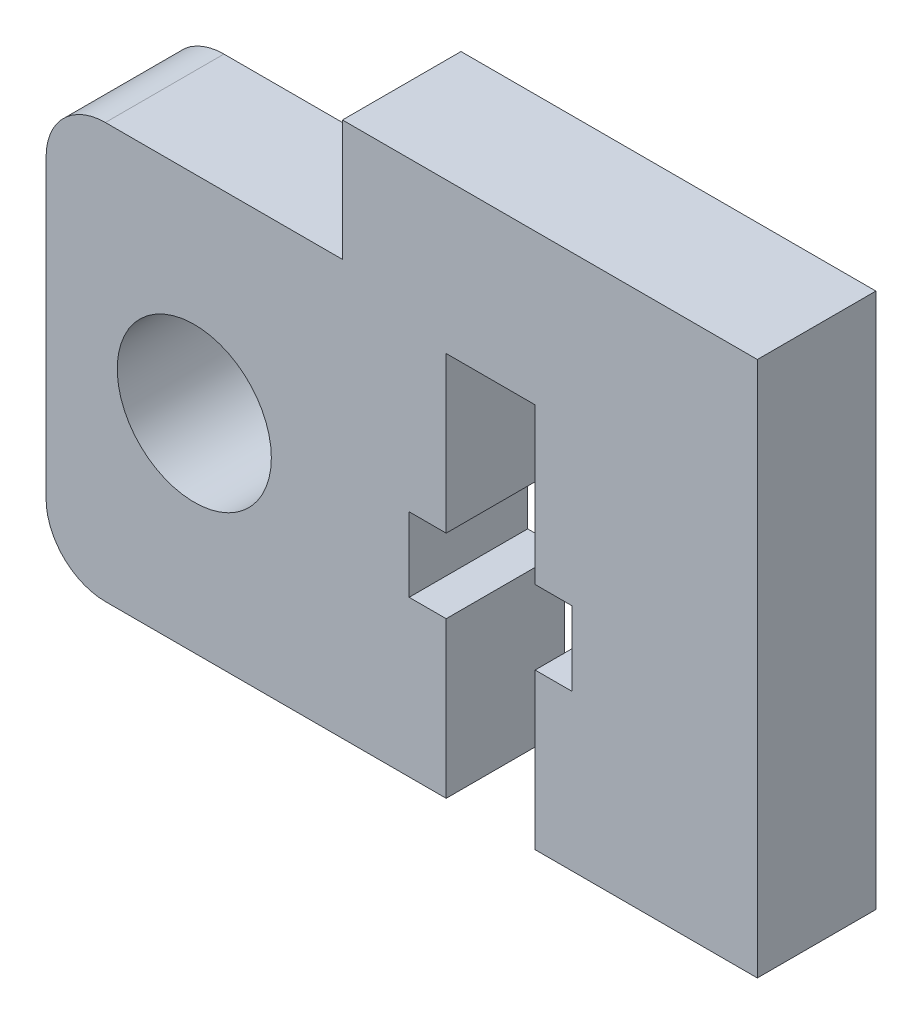
SolidWorks part; units mm, degrees
ref_plane "Спереди" through (0, 0, 0) normal (0, 0, 1) x (1, 0, 0)
ref_plane "Сверху" through (0, 0, 0) normal (0, 1, 0) x (1, 0, 0)
ref_plane "Справа" through (0, 0, 0) normal (1, 0, 0) x (0, 0, -1)
sketch "Эскиз1" plane through (0, 0, 0) normal (0, 0, 1) x (1, 0, 0)
  line L21 (14, 0) -> (14, 18.0747)
  line L33 (0, 0) -> (3.5, 0)
  line L51 (5, 18.0747) -> (0, 18.0747)
  line L58 (5, 18.0747) -> (14, 18.0747)
  line L59 (3.5, 0) -> (3.5, 5.25)
  line L60 (3.5, 5.25) -> (2.25, 5.25)
  line L61 (2.25, 5.25) -> (2.25, 7.75)
  line L62 (2.25, 7.75) -> (3.5, 7.75)
  line L63 (3.5, 7.75) -> (3.5, 13)
  line L64 (3.5, 13) -> (6.5, 13)
  line L65 (-8, 0) -> (0, 0)
  line L66 (6.5, 0) -> (6.5, 5.25)
  line L67 (7.75, 5.25) -> (7.75, 7.75)
  line L68 (6.5, 5.25) -> (7.75, 5.25)
  line L69 (7.75, 7.75) -> (6.5, 7.75)
  line L70 (6.5, 7.75) -> (6.5, 13)
  line L71 (6.5, 0) -> (14, 0)
  line L82 (0, 18.0747) -> (0, 14)
  line L83 (-8, 14) -> (0, 14)
  line L85 (-10, 12) -> (-10, 2)
  arc A2 (-10, 2) -> (-8, 0) centre (-8, 2) ccw
  arc A3 (-8, 14) -> (-10, 12) centre (-8, 12) ccw
  dimension "D7" = 2
  dimension "D8" = 14
  dimension "D3" = 2.5
  dimension "D2" = 13
  dimension "D1" = 14
  dimension "D4" = 5.5
  dimension "D5" = 3
  dimension "D6" = 2.5
extrude "Бобышка-Вытянуть1" add sketch "Эскиз1" along normal blind 4 contours L51 L82 L83 A3 L85 A2 L65 L33 L59 L60 L61 L62 L63 L64 L70 L69 L67 L68 L66 L71 L21 L58
sketch "Эскиз2" plane through (0, 0, 4) normal (0, 0, 1) x (1, 0, 0)
  line L0 (-10, 7) -> (0, 7) construction
  line L1 (-10, 12) -> (-10, 2) construction
  line L2 (-10, 12) -> (-10, 2) construction
  line L3 (-8, 14) -> (0, 14) construction
  circle A0 centre (-5, 7) radius 2.6
  dimension "D1" = 5.2
  dimension "D2" = 5.2
  dimension "D3" = 5
  dimension "D4" = 7
extrude "Вырез-Вытянуть1" cut sketch "Эскиз2" against normal blind 10
